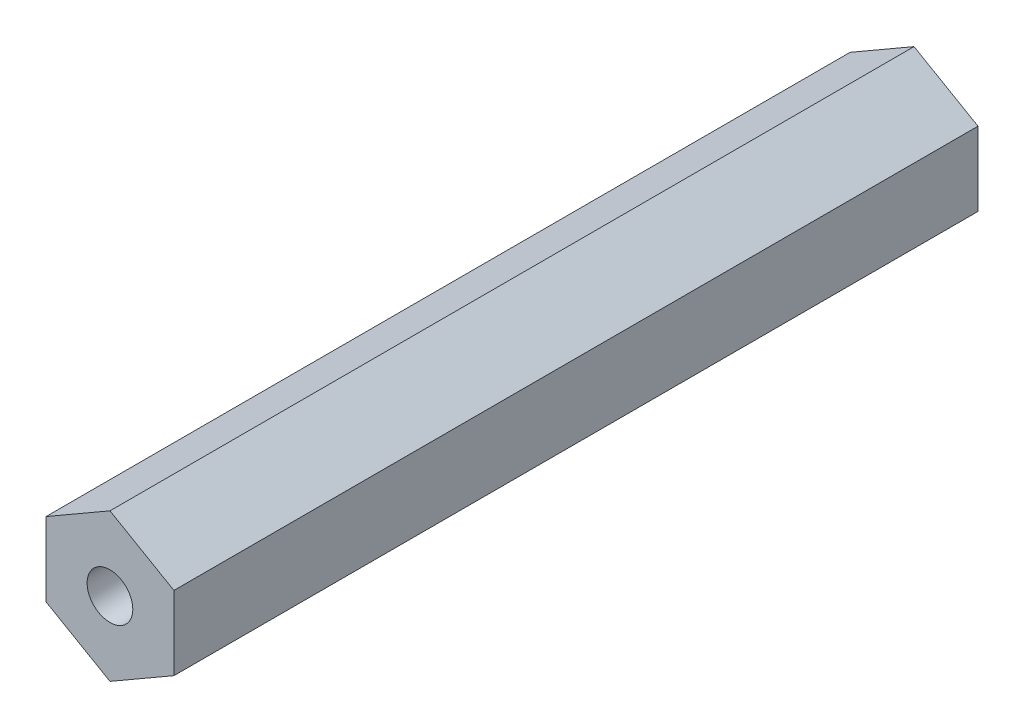
SolidWorks part; units mm, degrees
ref_plane "Front Plane" through (0, 0, 0) normal (0, 0, 1) x (1, 0, 0)
ref_plane "Top Plane" through (0, 0, 0) normal (0, 1, 0) x (1, 0, 0)
ref_plane "Right Plane" through (0, 0, 0) normal (1, 0, 0) x (0, 0, -1)
sketch "Sketch1" plane through (0, 0, 0) normal (0, 0, 1) x (1, 0, 0)
  line L0 (0, 4.0415) -> (0, 0) construction
  line L1 (0, -4.0415) -> (3.5, -2.0207)
  line L2 (3.5, -2.0207) -> (3.5, 2.0207)
  line L3 (3.5, 2.0207) -> (0, 4.0415)
  line L4 (0, 4.0415) -> (-3.5, 2.0207)
  line L5 (-3.5, 2.0207) -> (-3.5, -2.0207)
  line L6 (-3.5, -2.0207) -> (0, -4.0415)
  circle A0 centre (0, 0) radius 3.5 construction
extrude "Boss-Extrude1" add sketch "Sketch1" along normal blind 44
sketch "Sketch2" plane through (0, 0, 44) normal (0, 0, 1) x (1, 0, 0)
  circle A0 centre (0, 0) radius 1.25
extrude "Cut-Extrude1" cut sketch "Sketch2" against normal blind 5 contours A0
sketch "Sketch3" plane through (0, 0, 0) normal (0, 0, -1) x (-1, 0, 0)
  circle A0 centre (0, 0) radius 1.25
extrude "Cut-Extrude2" cut sketch "Sketch3" against normal blind 5
